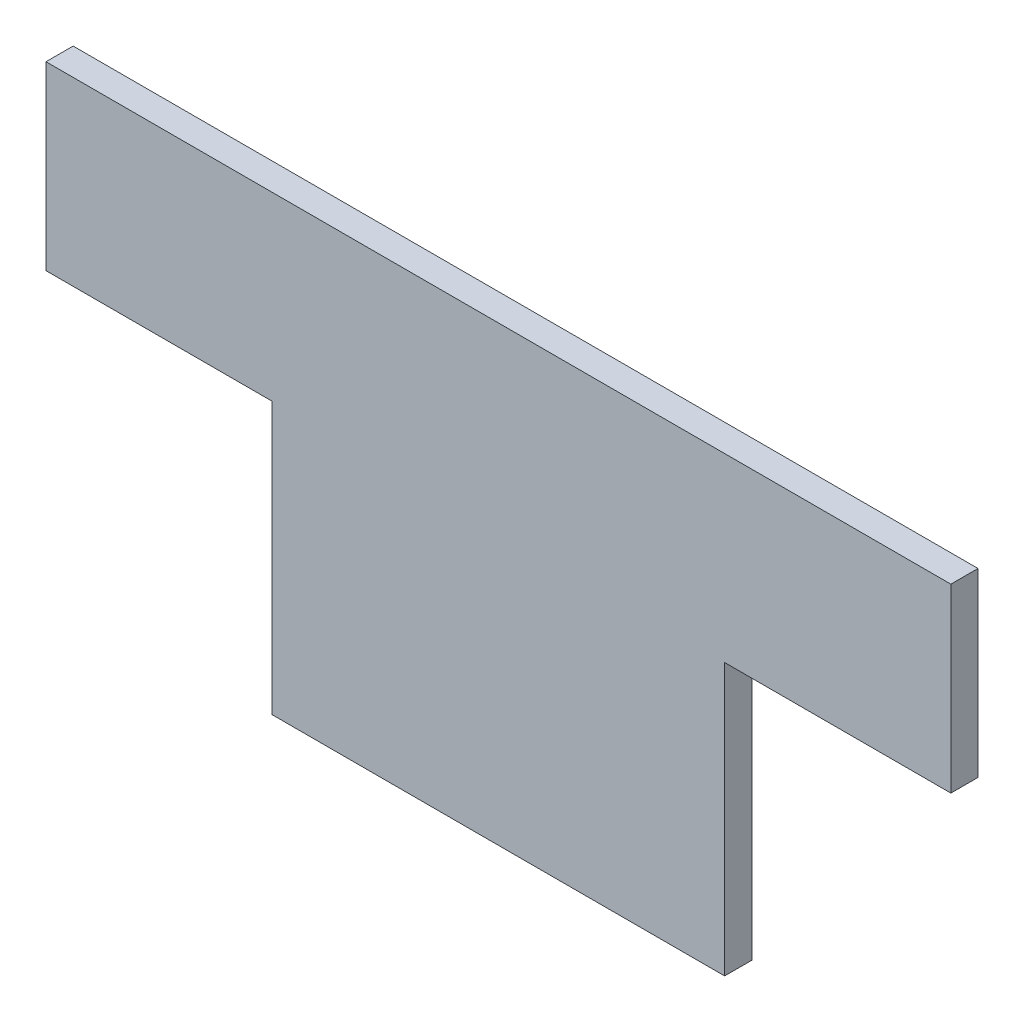
SolidWorks part; units mm, degrees
ref_plane "Front Plane" through (0, 0, 0) normal (0, 0, 1) x (1, 0, 0)
ref_plane "Top Plane" through (0, 0, 0) normal (0, 1, 0) x (1, 0, 0)
ref_plane "Right Plane" through (0, 0, 0) normal (1, 0, 0) x (0, 0, -1)
sketch "Sketch2" plane through (0, 0, 0) normal (0, 0, 1) x (1, 0, 0)
  line L0 (0, 25) -> (0, -25) construction
  line L1 (-50, 25) -> (50, 25)
  line L2 (-50, 25) -> (-50, 5)
  line L3 (-50, 5) -> (-25, 5)
  line L4 (50, 25) -> (50, 5)
  line L6 (-25, 5) -> (-25, -25)
  line L7 (-25, -25) -> (25, -25)
  line L8 (25, 5) -> (25, -25)
  line L9 (25, 5) -> (50, 5)
  point P10 (0, -25)
  point P11 (39.1831, 12.0213)
  point P12 (0, 0)
  point P14 (25, -32.8723)
  point P15 (25, -22.8487)
  point P16 (-25, 7.7273)
  dimension "D1" = 20
  dimension "D2" = 50
  dimension "D3" = 100
  dimension "D4" = 30
extrude "Boss-Extrude1" add sketch "Sketch2" along normal blind 3
